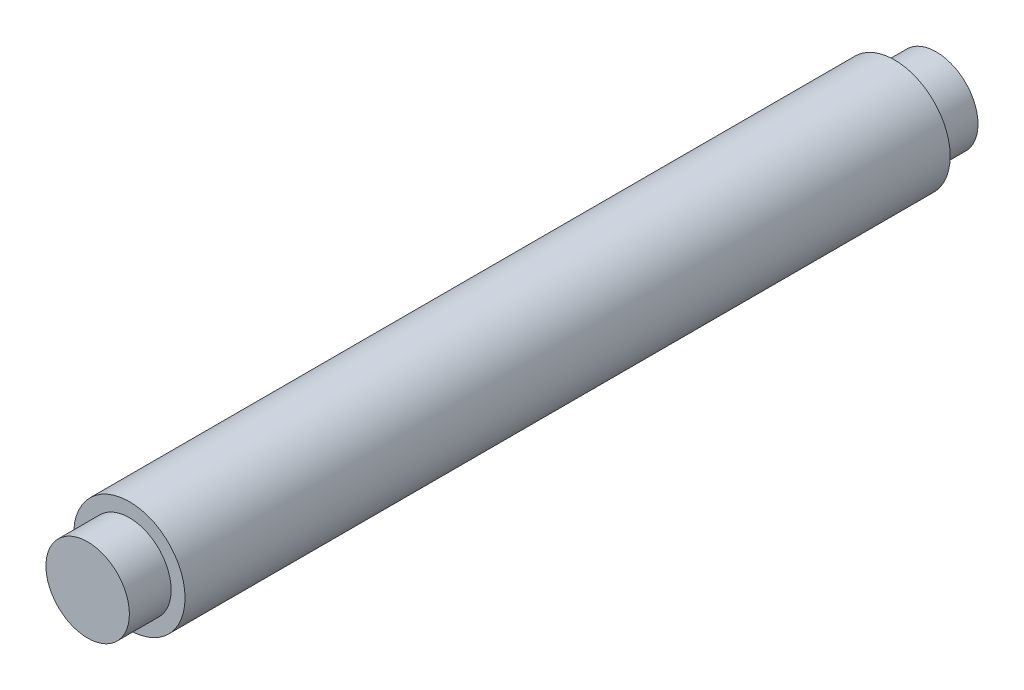
SolidWorks part; units mm, degrees
ref_plane "前视基准面" through (0, 0, 0) normal (0, 0, 1) x (1, 0, 0)
ref_plane "上视基准面" through (0, 0, 0) normal (0, 1, 0) x (1, 0, 0)
ref_plane "右视基准面" through (0, 0, 0) normal (1, 0, 0) x (0, 0, -1)
sketch "草图1" plane through (0, 0, 0) normal (0, 0, 1) x (1, 0, 0)
  circle A0 centre (0, 0) radius 4
  dimension "D1" = 8
extrude "凸台-拉伸1" add sketch "草图1" along normal blind 55
sketch "草图2" plane through (0, 0, 55) normal (0, 0, 1) x (1, 0, 0)
  circle A0 centre (0, 0) radius 3
  dimension "D1" = 6
extrude "凸台-拉伸2" add sketch "草图2" along normal blind 3
sketch "草图3" plane through (0, 0, 0) normal (0, 0, -1) x (-1, 0, 0)
  circle A0 centre (0, 0) radius 3
  dimension "D1" = 6
extrude "凸台-拉伸3" add sketch "草图3" along normal blind 3
